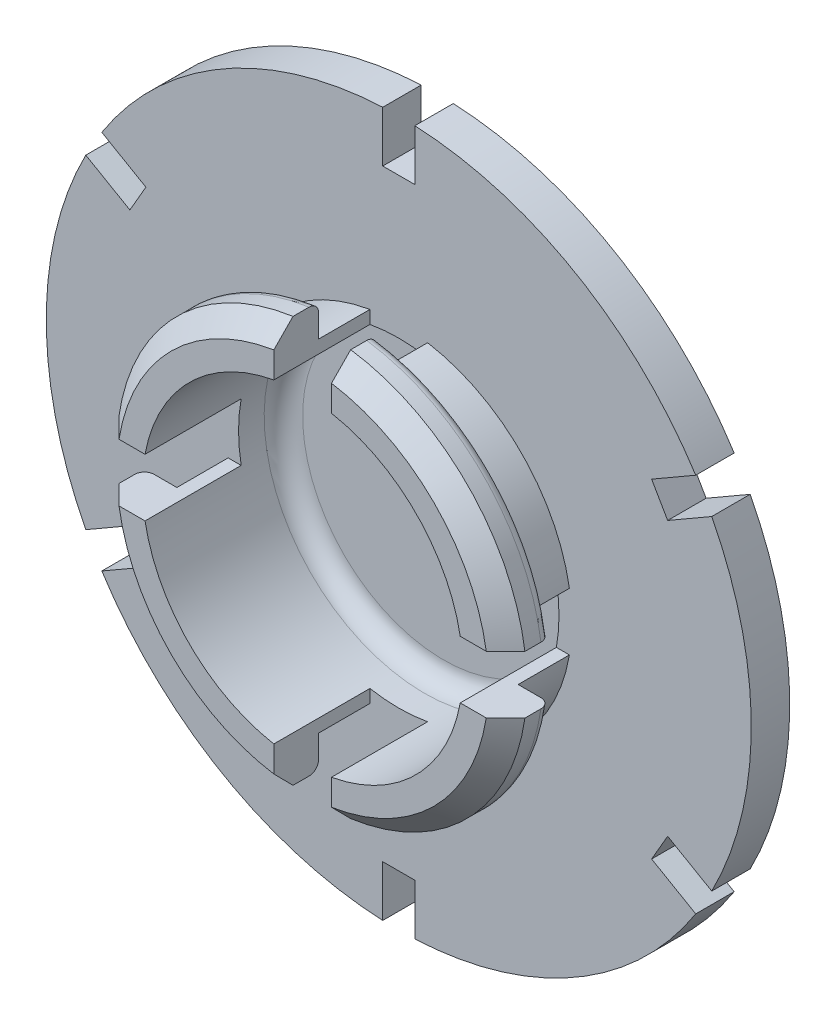
SolidWorks part; units mm, degrees
ref_plane "Front Plane" through (0, 0, 0) normal (0, 0, 1) x (1, 0, 0)
ref_plane "Top Plane" through (0, 0, 0) normal (0, 1, 0) x (1, 0, 0)
ref_plane "Right Plane" through (0, 0, 0) normal (1, 0, 0) x (0, 0, -1)
sketch "Sketch1" plane through (0, 0, 0) normal (0, 1, 0) x (1, 0, 0)
  line L0 (0, 11) -> (0, 14.5)
  line L1 (-12.5, 0) -> (-16, 0)
  line L2 (-16, 0) -> (-16, 3.5)
  line L3 (-27.5, 7.5) -> (-13.5, 7.5)
  line L4 (-27.5, 7.5) -> (-27.5, 10.5)
  line L5 (-27.5, 10.5) -> (-23.5, 10.5)
  line L6 (-16, 3.5) -> (-13.5, 3.5)
  line L7 (-13.5, 3.5) -> (-13.5, 7.5)
  line L8 (0, 14.5) -> (-13.0963, 14.5) construction
  line L9 (-12.5, 0) -> (-12.5, 11)
  line L10 (-12.5, 11) -> (0, 11)
  line L11 (0, 11) -> (0, 0) construction
  line L12 (-12.5, 0) -> (0, 0) construction
  arc A0 (-23.5, 10.5) -> (-6.9967, 14.1546) centre (0, -56.5313) cw
  arc A1 (-5.5026, 14.2865) -> (-6.9967, 14.1546) centre (-6.25, 14.2245) ccw
  arc A2 (-5.5026, 14.2865) -> (0, 14.5) centre (0, -56.5313) cw
  dimension "D3" = 27.5
  dimension "D7" = 1.5
  dimension "D13" = 3.5
  dimension "D1" = 11
  dimension "D2" = 3.5
  dimension "D4" = 3
  dimension "D5" = 4
  dimension "D6" = 2.5
  dimension "D8" = 6.25
  dimension "D9" = 4
  dimension "D10" = 12.5
  dimension "D11" = 12.5
  dimension "D12" = 16
revolve "Revolve1" add sketch "Sketch1" angle 360 about L11
chamfer "Chamfer1" distance 1.5 angle 45 1 edges at (-16, 0, 0)
fillet "Fillet1" radius 0.75 1 edges at (-16, 0, -3.5)
sketch "Sketch3" plane through (0, 0, -10.5) normal (0, 0, -1) x (-1, 0, 0)
  line L0 (1.25, 23.5) -> (1.25, 27.5)
  line L1 (1.25, 23.5) -> (-1.25, 23.5)
  line L2 (1.25, 27.5) -> (-1.25, 27.5)
  line L3 (-1.25, 23.5) -> (-1.25, 27.5)
  circle A2 centre (0, 0) radius 23.5 construction
  dimension "D1" = 2.5
  dimension "D2" = 4
extrude "Cut-Extrude2" cut sketch "Sketch3" against normal blind 10 contours L2 L3 L1 L0
pattern_circular "CirPattern1" count 6 over 360 about axis through (0, 0, 0) along (0, 0, 1) of "Cut-Extrude2"
sketch "Sketch4" plane through (0, 0, 0) normal (0, 0, 1) x (1, 0, 0)
  line L1 (2.25, 11.6649) -> (-2.25, 11.6649)
  line L2 (2.25, 11.6649) -> (2.25, 16.6649)
  line L3 (2.25, 16.6649) -> (-2.25, 16.6649)
  line L4 (-2.25, 11.6649) -> (-2.25, 16.6649)
  line L5 (2.25, 11.6649) -> (-2.25, 16.6649) construction
  line L6 (2.25, 16.6649) -> (-2.25, 11.6649) construction
  point P0 (0, 14.1649)
  dimension "D1" = 4.5
  dimension "D2" = 5
extrude "Cut-Extrude3" cut sketch "Sketch4" against normal blind 7.5
pattern_circular "CirPattern2" count 4 over 360 about axis through (0, 0, 0) along (0, 0, 1) of "Cut-Extrude3"
ref_plane "Plane1" through (0, 0, -20) normal (0, 0, 1) x (1, 0, 0)
sketch "Sketch7" plane through (0, 0, -20) normal (0, 0, 1) x (1, 0, 0)
  line L0 (0, 5.15) -> (0, -5.15) construction
  line L1 (4.3408, -0.833) -> (4.3408, 2.7123)
  line L2 (0.5562, 4.8332) -> (0.5562, 0.5376)
  line L3 (0.8062, 0.2876) -> (2.1277, 0.2876)
  line L4 (2.3648, -0.0417) -> (1.0217, -4.0572)
  line L5 (1.3062, 3.8472) -> (1.3062, 1.2876)
  line L6 (1.5562, 1.0376) -> (3.3408, 1.0376)
  line L7 (3.5908, 1.2876) -> (3.5908, 2.4785)
  line L8 (1.9237, -3.7249) -> (3.1774, 0.0232)
  line L9 (3.5908, -0.0403) -> (3.5908, -2.2517)
  line L10 (3.3908, 0.1597) -> (3.3671, 0.1597)
  line L11 (-0.798, 4.0551) -> (-0.798, -4.0551)
  line L12 (-4.5381, 1.5982) -> (-3.1169, 1.5982)
  line L13 (-2.8669, 1.8482) -> (-2.8669, 2.0982)
  line L14 (-3.1169, 2.3482) -> (-3.236, 2.3482)
  line L15 (-1.798, 0.375) -> (-2.3922, 0.375)
  line L16 (-2.6422, 0.625) -> (-2.6422, 0.8712)
  line L17 (-2.8922, 1.1212) -> (-3.1422, 1.1212)
  line L18 (-3.3922, 0.8712) -> (-3.3922, -0.0376)
  line L19 (0, 0) -> (-5.15, 0) construction
  line L20 (-2.6422, -0.625) -> (-2.6422, -0.8712)
  line L21 (-3.3922, -0.8712) -> (-3.3922, -0.0376)
  line L22 (-2.8922, -1.1212) -> (-3.1422, -1.1212)
  line L23 (-1.798, -0.375) -> (-2.3922, -0.375)
  line L24 (-4.5381, -1.5982) -> (-3.1169, -1.5982)
  line L25 (-2.8669, -1.8482) -> (-2.8669, -2.0982)
  line L26 (-3.1169, -2.3482) -> (-3.236, -2.3482)
  line L27 (-1.548, 3.7403) -> (-1.548, 0.625)
  line L28 (-1.548, -0.625) -> (-1.548, -3.7403)
  line L29 (-0.709, 4.944) -> (-0.5587, 4.7009)
  line L30 (-0.5787, 4.41) -> (-0.7405, 4.2145)
  line L31 (-0.5787, -4.41) -> (-0.7405, -4.2145)
  line L32 (-0.709, -4.944) -> (-0.5587, -4.7009)
  circle A0 centre (0, 0) radius 5.15 construction
  arc A1 (3.5522, 2.5965) -> (1.65, 4.0789) centre (0, 0) ccw
  arc A2 (0.6709, -5.1061) -> (2.1308, -4.6885) centre (0, 0) ccw
  arc A3 (3.618, -3.6651) -> (4.9423, -1.4479) centre (0, 0) ccw
  arc A4 (4.9423, -1.4479) -> (4.6383, -1.0935) centre (4.675, -1.3696) ccw
  arc A5 (4.6383, -1.0935) -> (4.3408, -0.833) centre (4.6036, -0.833) cw
  arc A6 (4.3081, 2.8219) -> (0.8473, 5.0798) centre (0, 0) ccw
  arc A7 (2.1308, -4.6885) -> (2.1766, -4.2163) centre (2.0174, -4.4392) ccw
  arc A8 (2.1766, -4.2163) -> (1.9237, -3.7249) centre (2.5275, -3.7249) cw
  arc A9 (1.0217, -4.0572) -> (0.5882, -4.73) centre (-0.8524, -3.3255) cw
  arc A10 (0.5882, -4.73) -> (0.6709, -5.1061) centre (0.7532, -4.8908) ccw
  arc A11 (2.1277, 0.2876) -> (2.3648, -0.0417) centre (2.1277, 0.0376) cw
  arc A12 (0.5562, 0.5376) -> (0.8062, 0.2876) centre (0.8062, 0.5376) ccw
  arc A13 (0.8473, 5.0798) -> (0.5562, 4.8332) centre (0.8062, 4.8332) ccw
  arc A14 (3.3408, 1.0376) -> (3.5908, 1.2876) centre (3.3408, 1.2876) ccw
  arc A15 (1.3062, 1.2876) -> (1.5562, 1.0376) centre (1.5562, 1.2876) ccw
  arc A16 (1.65, 4.0789) -> (1.3062, 3.8472) centre (1.5562, 3.8472) ccw
  arc A17 (3.5908, -0.0403) -> (3.3908, 0.1597) centre (3.3908, -0.0403) ccw
  arc A18 (3.1774, 0.0232) -> (3.3671, 0.1597) centre (3.3671, -0.0403) cw
  arc A19 (3.5908, -2.2517) -> (3.3414, -3.4892) centre (-0.8579, -1.999) cw
  arc A20 (3.3414, -3.4892) -> (3.618, -3.6651) centre (3.4998, -3.5454) ccw
  arc A21 (4.3408, 2.7123) -> (4.3081, 2.8219) centre (4.1408, 2.7123) ccw
  arc A22 (3.5522, 2.5965) -> (3.5908, 2.4785) centre (3.3908, 2.4785) cw
  arc A23 (-0.9687, 5.0581) -> (-4.7696, 1.9425) centre (0, 0) ccw
  arc A24 (-3.4309, 2.7547) -> (-1.9063, 3.9656) centre (0, 0) cw
  arc A25 (-3.4309, -2.7547) -> (-1.9063, -3.9656) centre (0, 0) ccw
  arc A26 (-0.798, -5.0878) -> (-4.7696, -1.9425) centre (0, 0) cw
  arc A27 (-4.5381, -1.5982) -> (-4.7696, -1.9425) centre (-4.5381, -1.8482) ccw
  arc A28 (-3.236, -2.3482) -> (-3.4309, -2.7547) centre (-3.236, -2.5982) ccw
  arc A29 (-2.6422, -0.8712) -> (-2.8922, -1.1212) centre (-2.8922, -0.8712) cw
  arc A30 (-3.3922, -0.8712) -> (-3.1422, -1.1212) centre (-3.1422, -0.8712) ccw
  arc A31 (-3.1422, 1.1212) -> (-3.3922, 0.8712) centre (-3.1422, 0.8712) ccw
  arc A32 (-2.6422, 0.8712) -> (-2.8922, 1.1212) centre (-2.8922, 0.8712) ccw
  arc A33 (-3.1169, 1.5982) -> (-2.8669, 1.8482) centre (-3.1169, 1.8482) ccw
  arc A34 (-2.8669, 2.0982) -> (-3.1169, 2.3482) centre (-3.1169, 2.0982) ccw
  arc A35 (-4.7696, 1.9425) -> (-4.5381, 1.5982) centre (-4.5381, 1.8482) ccw
  arc A36 (-3.4309, 2.7547) -> (-3.236, 2.3482) centre (-3.236, 2.5982) ccw
  arc A37 (-1.9063, -3.9656) -> (-1.548, -3.7403) centre (-1.798, -3.7403) ccw
  arc A38 (-1.548, 3.7403) -> (-1.9063, 3.9656) centre (-1.798, 3.7403) ccw
  arc A39 (-3.1169, -1.5982) -> (-2.8669, -1.8482) centre (-3.1169, -1.8482) cw
  arc A40 (-2.8669, -2.0982) -> (-3.1169, -2.3482) centre (-3.1169, -2.0982) cw
  arc A41 (-2.6422, -0.625) -> (-2.3922, -0.375) centre (-2.3922, -0.625) cw
  arc A42 (-2.3922, 0.375) -> (-2.6422, 0.625) centre (-2.3922, 0.625) cw
  arc A43 (-1.548, -0.625) -> (-1.798, -0.375) centre (-1.798, -0.625) ccw
  arc A44 (-1.548, 0.625) -> (-1.798, 0.375) centre (-1.798, 0.625) cw
  arc A45 (-0.709, 4.944) -> (-0.9687, 5.0581) centre (-0.9217, 4.8125) ccw
  arc A46 (-0.7405, 4.2145) -> (-0.798, 4.0551) centre (-0.548, 4.0551) ccw
  arc A47 (-0.5587, 4.7009) -> (-0.5787, 4.41) centre (-0.7713, 4.5694) cw
  arc A48 (-0.7405, -4.2145) -> (-0.798, -4.0551) centre (-0.548, -4.0551) cw
  arc A49 (-0.5587, -4.7009) -> (-0.5787, -4.41) centre (-0.7713, -4.5694) ccw
  arc A50 (-0.709, -4.944) -> (-0.9687, -5.0581) centre (-0.9217, -4.8125) cw
  point P38 (0.5562, 5.1199)
  point P41 (3.5908, 1.0376)
  point P55 (4.3408, 2.7713)
  point P84 (-4.8957, -1.5982)
  point P87 (-3.721, -2.3482)
  point P90 (-2.6422, -1.1212)
  point P93 (-3.3922, -1.1212)
  point P96 (-3.3922, 1.1212)
  point P99 (-2.6422, 1.1212)
  point P102 (-2.8669, 1.5982)
  point P105 (-2.8669, 2.3482)
  point P108 (-4.8957, 1.5982)
  point P111 (-3.721, 2.3482)
  point P116 (-2.8669, -1.5982)
  point P119 (-2.8669, -2.3482)
  point P122 (-2.6422, -0.375)
  point P125 (-2.6422, 0.375)
  point P134 (-0.798, 5.0878)
  dimension "D1" = 10.3
  dimension "D6" = 0.75
  dimension "D7" = 0.25
  dimension "D8" = 0.25
  dimension "D9" = 0.25
  dimension "D10" = 0.25
  dimension "D11" = 0.25
  dimension "D12" = 0.25
  dimension "D13" = 0.2
  dimension "D14" = 0.2
  dimension "D15" = 0.2
  dimension "D16" = 0.2
  dimension "D21" = 0.75
  dimension "D22" = 0.25
  dimension "D23" = 0.25
  dimension "D24" = 0.25
  dimension "D25" = 0.25
  dimension "D26" = 0.25
  dimension "D27" = 0.25
  dimension "D28" = 0.25
  dimension "D29" = 0.25
  dimension "D30" = 0.25
  dimension "D31" = 0.25
  dimension "D32" = 0.25
  dimension "D33" = 0.25
  dimension "D34" = 0.25
  dimension "D35" = 0.25
  dimension "D36" = 0.25
  dimension "D37" = 0.25
  dimension "D38" = 0.25
  dimension "D39" = 0.25
  dimension "D40" = 0.25
  dimension "D41" = 0.25
  dimension "D42" = 0.25
  dimension "D2" = 0.75
  dimension "D3" = 0.75
  dimension "D4" = 0.75
  dimension "D5" = 0.75
  dimension "D17" = 0.375
  dimension "D18" = 0.75
  dimension "D19" = 0.75
  dimension "D20" = 0.75
extrude "Cut-Extrude4" cut sketch "Sketch7" along normal blind 6.5 contours A50 L32 A49 L31 A48 L11 A46 L30 A47 L29 A45 A23 A35 L12 A33 L13 A34 L14 A36 A24 A38 L27 A44 L15 A42 L16 A32 L17 A31 L18 L21 A30 L22 A29 L20 A41 L23 A43 L28 A37 A25 A28 L26 A40 L25 A39 L24 A27 A26 | L1 A21 A6 A13 L2 A12 L3 A11 L4 A9 A10 A2 A7 A8 L8 A18 L10 A17 L9 A19 A20 A3 A4 A5 | L7 A22 A1 A16 L5 A15 L6 A14
fillet "Fillet2" radius 1.5 1 edges at (-12.5, 0, -11)
